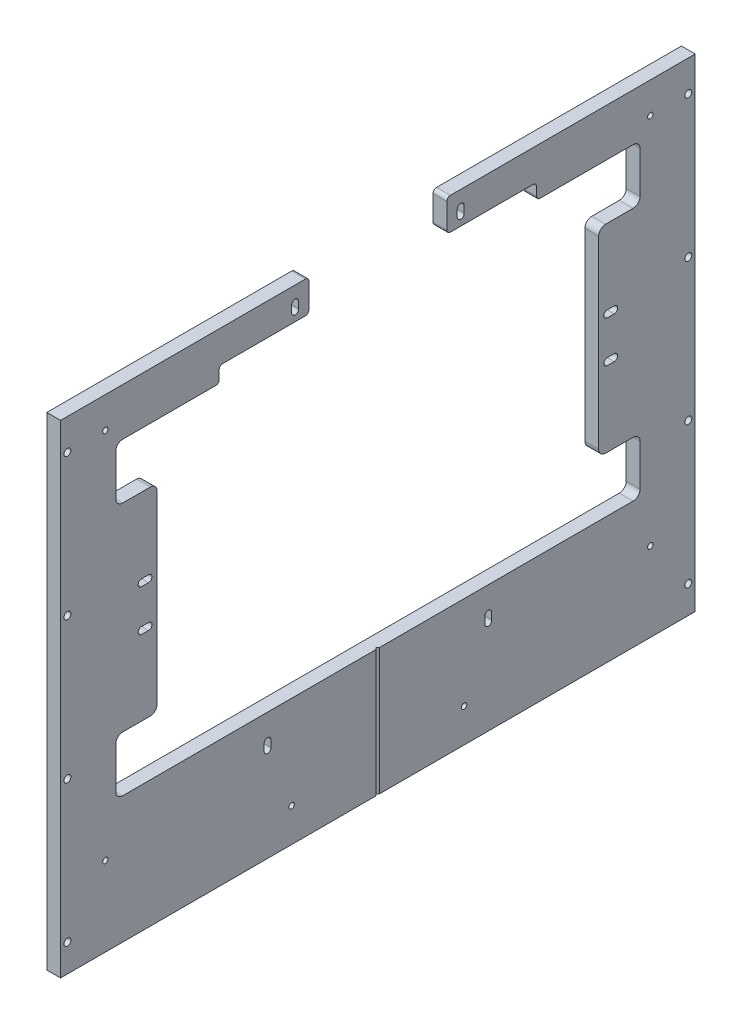
SolidWorks part; units mm, degrees
material "Alum 6061 (Default)"
ref_plane "Front Plane" through (0, 0, 0) normal (0, 0, 1) x (1, 0, 0)
ref_plane "Top Plane" through (0, 0, 0) normal (0, 1, 0) x (1, 0, 0)
ref_plane "Right Plane" through (0, 0, 0) normal (1, 0, 0) x (0, 0, -1)
sketch "Sketch10" plane through (0, 0, 0) normal (1, 0, 0) x (0, 0, -1)
  line L0 (-146.05, 36.5125) -> (146.05, 36.5125) construction
  line L1 (146.05, -80.1688) -> (-146.05, -80.1688)
  line L2 (146.05, -80.1688) -> (146.05, 153.1937)
  line L3 (146.05, 153.1937) -> (-146.05, 153.1937)
  line L4 (-146.05, -80.1688) -> (-146.05, 153.1937)
  line L5 (146.05, -80.1688) -> (-146.05, 153.1937) construction
  line L6 (146.05, 153.1937) -> (-146.05, -80.1688) construction
  point P0 (0, 36.5125)
  point P8 (0, 153.1937)
  dimension "D1" = 153.1937
  dimension "MainC" = 292.1
  dimension "MainD" = 233.3625
sketch "Sketch24" plane through (0, 0, 0) normal (1, 0, 0) x (0, 0, -1)
  line L1 (-146.05, -80.1688) -> (146.05, -80.1688)
  line L2 (-146.05, -80.1688) -> (-146.05, 153.1937)
  line L3 (-146.05, 153.1937) -> (146.05, 153.1937)
  line L4 (146.05, -80.1688) -> (146.05, 153.1937)
  line L5 (-146.05, -80.1688) -> (146.05, 153.1937) construction
  line L6 (-146.05, 153.1937) -> (146.05, -80.1688) construction
  point P0 (0, 36.5125)
sketch3d "3DSketch1"
  point P0 (0, 153.1937, 146.05)
  point P1 (0, -80.1688, 146.05)
  dimension "D2" = 146.05
  dimension "D1" = 146.05
sketch3d "3DSketch2"
  point P0 (0, 153.1937, -146.05)
  point P1 (0, -80.1688, -146.05)
  dimension "D2" = 146.05
  dimension "D1" = 146.05
sketch "Sketch1" plane through (0, 0, 0) normal (0, 0, 1) x (1, 0, 0)
  line L0 (0, -80.1688) -> (0, -222.25) construction
  line L1 (-6.35, 222.25) -> (6.35, 222.25)
  line L2 (-6.35, 222.25) -> (-6.35, -222.25)
  line L3 (-6.35, -222.25) -> (6.35, -222.25)
  line L4 (6.35, 222.25) -> (6.35, -222.25)
  line L5 (-6.35, 222.25) -> (6.35, -222.25) construction
  line L6 (-6.35, -222.25) -> (6.35, 222.25) construction
  point P0 (0, 0)
  point P2 (1.2269, 222.25)
  point P7 (0, -222.25)
  dimension "D1" = 69.0563
  dimension "Width" = 12.7
  dimension "D2" = 142.0812
extrude "Extrude1" add sketch "Sketch1" along normal up to surface (292.1 mm away) and the other way up to surface (292.1 mm away)
sketch "Sketch4" plane through (6.35, 0, 0) normal (1, 0, 0) x (0, 0, -1)
  line L0 (203.2, 127.7937) -> (241.3, 127.7937)
  line L2 (-203.2, 127.7937) -> (-203.2, -54.7688)
  line L3 (-241.3, -105.5688) -> (241.3, -105.5688)
  line L4 (203.2, 127.7937) -> (203.2, -54.7688)
  line L5 (-241.3, 178.5937) -> (241.3, 178.5937)
  line L6 (-241.3, 178.5937) -> (-241.3, 127.7937)
  line L7 (-241.3, 127.7937) -> (-203.2, 127.7937)
  line L8 (241.3, 178.5937) -> (241.3, 127.7937)
  line L9 (0, -105.5688) -> (0, 178.5937) construction
  line L10 (203.2, -54.7688) -> (241.3, -54.7688)
  line L11 (241.3, -54.7688) -> (241.3, -105.5688)
  line L12 (-203.2, -54.7688) -> (-241.3, -54.7688)
  line L13 (-241.3, -54.7688) -> (-241.3, -105.5688)
  line L17 (146.05, -80.1688) -> (146.05, 153.1937) construction
  line L19 (-146.05, -80.1688) -> (146.05, -80.1688) construction
  line L20 (-146.05, -80.1688) -> (-146.05, 153.1937) construction
  line L21 (292.1, 193.9593) -> (292.1, -82.6467) construction
  dimension "D2" = 57.15
  dimension "D3" = 50.8
  dimension "D4" = 50.8
  dimension "D5" = 25.4
  dimension "D6" = 25.4
  dimension "D7" = 25.4
  dimension "D8" = 57.15
extrude "Cut-Extrude1" cut sketch "Sketch4" against normal up to next
sketch "Sketch5" plane through (6.35, 0, 0) normal (1, 0, 0) x (0, 0, -1)
  line L6 (-63.5, 222.25) -> (-63.5, 178.5937)
  line L7 (-63.5, 178.5937) -> (63.5, 178.5937)
  line L8 (63.5, 222.25) -> (63.5, 178.5937)
  line L9 (-63.5, 222.25) -> (63.5, 222.25)
  line L17 (241.3, 178.5937) -> (-241.3, 178.5937) construction
  line L18 (88.9, 153.1937) -> (88.9, 205.8796) construction
  line L19 (-146.05, 153.1937) -> (146.05, 153.1937) construction
  line L20 (88.9, 205.8796) -> (63.5, 205.8796) construction
  line L27 (-292.1, 222.25) -> (292.1, 222.25) construction
  point P4 (0, 222.25)
  point P8 (0, 178.5937)
  dimension "D1" = 25.4
  dimension "D2" = 52.6859
  dimension "D3" = 127
extrude "Cut-Extrude2" cut sketch "Sketch5" against normal up to next
fillet "Fillet2" radius 6.35 12 edges at (0, 178.5937, 241.3) (0, 178.5937, -241.3) (0, 127.7937, -241.3) (0, 127.7937, 241.3) (0, 127.7937, -203.2) (0, 127.7937, 203.2) (0, -54.7688, 203.2) (0, -54.7688, -203.2) (0, -54.7688, -241.3) (0, -105.5688, -241.3) (0, -105.5688, 241.3) (0, -54.7688, 241.3)
hole_wizard "M6x1.0 Tapped Hole1" positions "Sketch9" profile "Sketch8" tap size "M6x1.0" standard "ANSI Metric" end condition up to next
sketch "Sketch9" plane through (6.35, 0, 0) normal (1, 0, 0) x (0, 0, -1)
  line L0 (-76.2, 204.7875) -> (76.2, 204.7875) construction
  line L5 (-101.6, -132.2388) -> (101.6, -132.2388) construction
  line L15 (146.05, 153.1937) -> (-146.05, 153.1937) construction
  line L16 (146.05, -80.1688) -> (-146.05, -80.1688) construction
  line L25 (0, 204.7875) -> (0, 0) construction
  point P0 (76.2, 204.7875)
  point P2 (-76.2, 204.7875)
  point P17 (101.6, -132.2388)
  point P20 (-101.6, -132.2388)
  point P86 (0, 204.7875)
  point P92 (0, -132.2388)
  dimension "D1" = 152.4
  dimension "D2" = 51.5938
  dimension "D3" = 203.2
  dimension "D5" = 52.07
other "AlignGroup1"
sketch "Sketch8" plane through (6.35, 204.7875, -76.2) normal (0, 1, 0) x (0, 0, -1)
  line L0 (0, 0) -> (0, 12.7)
  line L1 (0, 12.7) -> (2.5, 12.7)
  line L2 (2.5, 12.7) -> (2.5, 0)
  line L5 (2.5, 0) -> (0, 0)
  line L11 (0, -6.35) -> (0, 107.95) construction
  dimension "Thru Tap Drill Dia." = 5
  dimension "Thru Tap Drill Depth" = 12.7
cosmetic thread "Hole Thread11" parameters "D2"=6
cosmetic thread "Hole Thread12" parameters "D2"=6
cosmetic thread "Hole Thread41" parameters "D2"=6
cosmetic thread "Hole Thread42" parameters "D2"=6
sketch "Sketch11" plane through (6.35, 0, 0) normal (1, 0, 0) x (0, 0, -1)
  line L0 (234.95, 178.5937) -> (63.5, 178.5937) construction
  line L1 (-146.05, 178.5937) -> (146.05, 178.5937)
  line L2 (-146.05, 178.5937) -> (-146.05, 192.8812)
  line L3 (-146.05, 192.8812) -> (146.05, 192.8812)
  line L4 (146.05, 178.5937) -> (146.05, 192.8812)
  line L5 (292.1, 193.9593) -> (292.1, -82.6467) construction
  circle A0 centre (-76.2, 204.7875) radius 2.5 construction
  point P6 (0, 178.5937)
  dimension "D2" = 11.9062
  dimension "D3" = 146.05
extrude "Cut-Extrude3" cut sketch "Sketch11" against normal through all
fillet "Fillet3" radius 3.175 8 edges at (0, 222.25, -63.5) (0, 222.25, 63.5) (0, 178.5937, -146.05) (0, 192.8812, -146.05) (0, 178.5937, 146.05) (0, 192.8812, -63.5) (0, 192.8812, 63.5) (0, 192.8812, 146.05)
sketch "Sketch19" plane through (6.35, 0, 0) normal (1, 0, 0) x (0, 0, -1)
  line L12 (76.2, 207.9625) -> (76.2, 201.6125) construction
  line L13 (79.375, 207.9625) -> (79.375, 201.6125)
  line L14 (73.025, 207.9625) -> (73.025, 201.6125)
  line L15 (-76.2, 207.9625) -> (-76.2, 201.6125) construction
  line L16 (-73.025, 207.9625) -> (-73.025, 201.6125)
  line L17 (-79.375, 207.9625) -> (-79.375, 201.6125)
  line L18 (-101.6, -129.0638) -> (-101.6, -135.4138) construction
  line L19 (-98.425, -129.0638) -> (-98.425, -135.4138)
  line L20 (-104.775, -129.0638) -> (-104.775, -135.4138)
  line L21 (101.6, -129.0638) -> (101.6, -135.4138) construction
  line L22 (104.775, -129.0638) -> (104.775, -135.4138)
  line L23 (98.425, -129.0638) -> (98.425, -135.4138)
  arc A8 (79.375, 207.9625) -> (73.025, 207.9625) centre (76.2, 207.9625) ccw
  arc A9 (73.025, 201.6125) -> (79.375, 201.6125) centre (76.2, 201.6125) ccw
  arc A10 (-73.025, 207.9625) -> (-79.375, 207.9625) centre (-76.2, 207.9625) ccw
  arc A11 (-79.375, 201.6125) -> (-73.025, 201.6125) centre (-76.2, 201.6125) ccw
  arc A12 (-98.425, -129.0638) -> (-104.775, -129.0638) centre (-101.6, -129.0638) ccw
  arc A13 (-104.775, -135.4138) -> (-98.425, -135.4138) centre (-101.6, -135.4138) ccw
  arc A14 (104.775, -129.0638) -> (98.425, -129.0638) centre (101.6, -129.0638) ccw
  arc A15 (98.425, -135.4138) -> (104.775, -135.4138) centre (101.6, -135.4138) ccw
  point P33 (76.2, 204.7875)
  point P41 (-76.2, 204.7875)
  point P49 (-101.6, -132.2388)
  point P57 (101.6, -132.2388)
  dimension "D1" = 6.35
  dimension "D2" = 6.35
extrude "Cut-Extrude8" cut sketch "Sketch19" against normal up to next
sketch "Sketch18" plane through (0, -222.25, 0) normal (0, -1, 0) x (1, 0, 0)
  line L3 (6.35, 1.5875) -> (6.35, -1.5875)
  line L4 (6.35, -1.5875) -> (4.7625, 0)
  line L5 (4.7625, 0) -> (6.35, 1.5875)
  line L6 (6.35, 292.1) -> (6.35, -292.1) construction
  point P2 (6.35, 0)
  dimension "D1" = 3.175
  dimension "D2" = 1.5875
extrude "Cut-Extrude7" cut sketch "Sketch18" against normal through all both and the other way through all
hole_wizard "M6x1.0 Tapped Hole2" positions "Sketch20" profile "Sketch21" tap size "M6x1.0" standard "ANSI Metric" end condition up to next
sketch "Sketch20" plane through (6.35, 0, 0) normal (1, 0, 0) x (0, 0, -1)
  line L0 (-146.05, -80.1688) -> (-146.05, 153.1937) construction
  line L1 (146.05, -80.1688) -> (146.05, 153.1937) construction
  line L3 (-250.825, 193.675) -> (-250.825, -149.225) construction
  line L5 (-250.825, 22.225) -> (-170.837, 22.225) construction
  line L9 (-79.375, -191.2938) -> (79.375, -191.2938) construction
  line L11 (-292.1, 125.73) -> (-292.1, -125.73) construction
  line L12 (-146.05, -80.1688) -> (146.05, -80.1688) construction
  point P0 (79.375, -191.2938)
  point P3 (-79.375, -191.2938)
  point P6 (250.825, -149.225)
  point P9 (250.825, 193.675)
  point P12 (-250.825, 193.675)
  point P15 (-250.825, -149.225)
  point P43 (0, -191.2938)
  dimension "D1" = 104.775
  dimension "D2" = 104.775
  dimension "D3" = 40.4813
  dimension "D5" = 212.725
  dimension "D6" = 111.125
  dimension "D7" = 69.0562
sketch "Sketch21" plane through (6.35, -191.2938, -79.375) normal (0, 1, 0) x (0, 0, -1)
  line L0 (0, 0) -> (0, 12.7)
  line L1 (0, 12.7) -> (2.5, 12.7)
  line L2 (2.5, 12.7) -> (2.5, 0)
  line L5 (2.5, 0) -> (0, 0)
  line L11 (0, -6.35) -> (0, 107.95) construction
  dimension "Thru Tap Drill Dia." = 5
  dimension "Thru Tap Drill Depth" = 12.7
cosmetic thread "Hole Thread39" parameters "D2"=6
cosmetic thread "Hole Thread40" parameters "D2"=6
cosmetic thread "Hole Thread44" parameters "D2"=6
cosmetic thread "Hole Thread45" parameters "D2"=6
cosmetic thread "Hole Thread48" parameters "D2"=6
cosmetic thread "Hole Thread49" parameters "D2"=6
hole_wizard "M6 Clearance Hole1" positions "Sketch22" profile "Sketch23" hole size "M6" standard "ANSI Metric" end condition up to next
sketch "Sketch22" plane through (6.35, 0, 0) normal (1, 0, 0) x (0, 0, -1)
  line L0 (-292.1, 222.25) -> (-66.675, 222.25) construction
  line L1 (-292.1, -222.25) -> (-292.1, 222.25) construction
  line L2 (292.1, -222.25) -> (292.1, 222.25) construction
  line L3 (-292.1, -222.25) -> (292.1, -222.25) construction
  line L4 (-285.75, 193.675) -> (-285.75, 63.5) construction
  line L5 (-285.75, 63.5) -> (-285.75, -66.675) construction
  line L6 (-285.75, -66.675) -> (-285.75, -196.85) construction
  point P0 (-285.75, -196.85)
  point P2 (-285.75, -66.675)
  point P4 (-285.75, 193.675)
  point P6 (-285.75, 63.5)
  point P15 (285.75, 193.675)
  point P17 (285.75, 63.5)
  point P19 (285.75, -66.675)
  point P21 (285.75, -196.85)
  dimension "D1" = 28.575
  dimension "D5" = 6.35
  dimension "D6" = 6.35
  dimension "D7" = 25.4
sketch "Sketch23" plane through (6.35, -196.85, 285.75) normal (0, 1, 0) x (0, 0, -1)
  line L0 (0, 0) -> (0, 12.7)
  line L1 (0, 12.7) -> (3.2, 12.7)
  line L2 (3.2, 12.7) -> (3.2, 0)
  line L5 (3.2, 0) -> (0, 0)
  line L11 (0, -6.35) -> (0, 107.95) construction
  dimension "Thru Hole Dia." = 6.4
  dimension "Thru Hole Depth" = 12.7
sketch "Sketch25" plane through (-6.35, 0, 0) normal (-1, 0, 0) x (0, 0, 1)
  point P0 (250.825, 193.675)
  point P1 (250.825, -149.225)
sketch "Sketch26" plane through (6.35, 0, 0) normal (1, 0, 0) x (0, 0, -1)
  line L0 (0, 36.5125) -> (-214.3125, 36.5125) construction
  line L1 (-203.2, 121.4437) -> (-203.2, -48.4188) construction
  line L2 (-214.3125, 17.4625) -> (-214.3125, 55.5625) construction
  line L3 (0, 36.5125) -> (214.3125, 36.5125) construction
  line L4 (203.2, -48.4188) -> (203.2, 121.4437) construction
  line L5 (214.3125, 55.5625) -> (214.3125, 17.4625) construction
  point P7 (-214.3125, 36.5125)
  point P13 (214.3125, 36.5125)
  dimension "D1" = 11.1125
  dimension "D2" = 38.1
  dimension "D3" = 11.1125
  dimension "D4" = 38.1
hole_wizard "M6x1.0 Tapped Hole3" positions "3DSketch3" profile "Sketch27" tap size "M6x1.0" standard "ANSI Metric" end condition up to next
sketch3d "3DSketch3"
  point P0 (6.35, 55.5625, 214.3125)
  point P3 (6.35, 17.4625, 214.3125)
  point P6 (6.35, 55.5625, -214.3125)
  point P9 (6.35, 17.4625, -214.3125)
sketch "Sketch27" plane through (6.35, 55.5625, 214.3125) normal (0, 1, 0) x (0, 0, -1)
  line L0 (0, 0) -> (0, 12.7)
  line L1 (0, 12.7) -> (2.5, 12.7)
  line L2 (2.5, 12.7) -> (2.5, 0)
  line L5 (2.5, 0) -> (0, 0)
  line L11 (0, -6.35) -> (0, 107.95) construction
  dimension "Thru Tap Drill Dia." = 5
  dimension "Thru Tap Drill Depth" = 12.7
cosmetic thread "Hole Thread50" parameters "D2"=6
cosmetic thread "Hole Thread51" parameters "D2"=6
cosmetic thread "Hole Thread52" parameters "D2"=6
cosmetic thread "Hole Thread53" parameters "D2"=6
sketch "Sketch28" plane through (6.35, 0, 0) normal (1, 0, 0) x (0, 0, -1)
  line L0 (-217.4875, 17.4625) -> (-211.1375, 17.4625) construction
  line L1 (-217.4875, 20.6375) -> (-211.1375, 20.6375)
  line L2 (-217.4875, 14.2875) -> (-211.1375, 14.2875)
  line L3 (-217.4875, 55.5625) -> (-211.1375, 55.5625) construction
  line L4 (-217.4875, 58.7375) -> (-211.1375, 58.7375)
  line L5 (-73.025, 201.6125) -> (-73.025, 207.9625)
  line L6 (-79.375, 207.9625) -> (-79.375, 201.6125)
  line L7 (-73.025, 201.6125) -> (-73.025, 207.9625)
  line L8 (-79.375, 207.9625) -> (-79.375, 201.6125)
  line L9 (79.375, 201.6125) -> (79.375, 207.9625)
  line L10 (73.025, 207.9625) -> (73.025, 201.6125)
  line L11 (79.375, 201.6125) -> (79.375, 207.9625)
  line L12 (73.025, 207.9625) -> (73.025, 201.6125)
  line L13 (104.775, -135.4138) -> (104.775, -129.0638)
  line L14 (98.425, -129.0638) -> (98.425, -135.4138)
  line L15 (104.775, -135.4138) -> (104.775, -129.0638)
  line L16 (98.425, -129.0638) -> (98.425, -135.4138)
  line L17 (-98.425, -135.4138) -> (-98.425, -129.0638)
  line L18 (-104.775, -129.0638) -> (-104.775, -135.4138)
  line L19 (-98.425, -135.4138) -> (-98.425, -129.0638)
  line L20 (-104.775, -129.0638) -> (-104.775, -135.4138)
  line L21 (-217.4875, 52.3875) -> (-211.1375, 52.3875)
  line L22 (211.1375, 55.5625) -> (217.4875, 55.5625) construction
  line L23 (211.1375, 58.7375) -> (217.4875, 58.7375)
  line L24 (211.1375, 52.3875) -> (217.4875, 52.3875)
  line L25 (211.1375, 17.4625) -> (217.4875, 17.4625) construction
  line L26 (211.1375, 20.6375) -> (217.4875, 20.6375)
  line L27 (211.1375, 14.2875) -> (217.4875, 14.2875)
  arc A0 (-217.4875, 20.6375) -> (-217.4875, 14.2875) centre (-217.4875, 17.4625) ccw
  arc A1 (-211.1375, 14.2875) -> (-211.1375, 20.6375) centre (-211.1375, 17.4625) ccw
  arc A2 (211.1375, 20.6375) -> (211.1375, 14.2875) centre (211.1375, 17.4625) ccw
  arc A3 (-217.4875, 58.7375) -> (-217.4875, 52.3875) centre (-217.4875, 55.5625) ccw
  arc A4 (-211.1375, 52.3875) -> (-211.1375, 58.7375) centre (-211.1375, 55.5625) ccw
  arc A5 (-79.375, 201.6125) -> (-73.025, 201.6125) centre (-76.2, 201.6125) ccw
  arc A6 (-73.025, 207.9625) -> (-79.375, 207.9625) centre (-76.2, 207.9625) ccw
  arc A7 (-79.375, 201.6125) -> (-73.025, 201.6125) centre (-76.2, 201.6125) ccw
  arc A8 (-73.025, 207.9625) -> (-79.375, 207.9625) centre (-76.2, 207.9625) ccw
  arc A9 (73.025, 201.6125) -> (79.375, 201.6125) centre (76.2, 201.6125) ccw
  arc A10 (79.375, 207.9625) -> (73.025, 207.9625) centre (76.2, 207.9625) ccw
  arc A11 (73.025, 201.6125) -> (79.375, 201.6125) centre (76.2, 201.6125) ccw
  arc A12 (79.375, 207.9625) -> (73.025, 207.9625) centre (76.2, 207.9625) ccw
  arc A13 (98.425, -135.4138) -> (104.775, -135.4138) centre (101.6, -135.4138) ccw
  arc A14 (104.775, -129.0638) -> (98.425, -129.0638) centre (101.6, -129.0638) ccw
  arc A15 (98.425, -135.4138) -> (104.775, -135.4138) centre (101.6, -135.4138) ccw
  arc A16 (104.775, -129.0638) -> (98.425, -129.0638) centre (101.6, -129.0638) ccw
  arc A17 (-104.775, -135.4138) -> (-98.425, -135.4138) centre (-101.6, -135.4138) ccw
  arc A18 (-98.425, -129.0638) -> (-104.775, -129.0638) centre (-101.6, -129.0638) ccw
  arc A19 (-104.775, -135.4138) -> (-98.425, -135.4138) centre (-101.6, -135.4138) ccw
  arc A20 (-98.425, -129.0638) -> (-104.775, -129.0638) centre (-101.6, -129.0638) ccw
  arc A21 (211.1375, 58.7375) -> (211.1375, 52.3875) centre (211.1375, 55.5625) ccw
  arc A22 (217.4875, 52.3875) -> (217.4875, 58.7375) centre (217.4875, 55.5625) ccw
  arc A23 (217.4875, 14.2875) -> (217.4875, 20.6375) centre (217.4875, 17.4625) ccw
  point P2 (-214.3125, 17.4625)
  point P9 (214.3125, 55.5625)
  point P43 (-214.3125, 55.5625)
  point P48 (214.3125, 17.4625)
  dimension "D6" = 3.175
  dimension "D9" = 3.175
  dimension "D10" = 3.175
  dimension "D11" = 3.175
  dimension "D5" = 6.35
  dimension "D7" = 6.35
  dimension "D8" = 6.35
  dimension "D12" = 6.35
  dimension "D1" = 0
  dimension "D2" = 0
  dimension "D3" = 0
  dimension "D4" = 0
extrude "Cut-Extrude9" cut sketch "Sketch28" against normal through all
